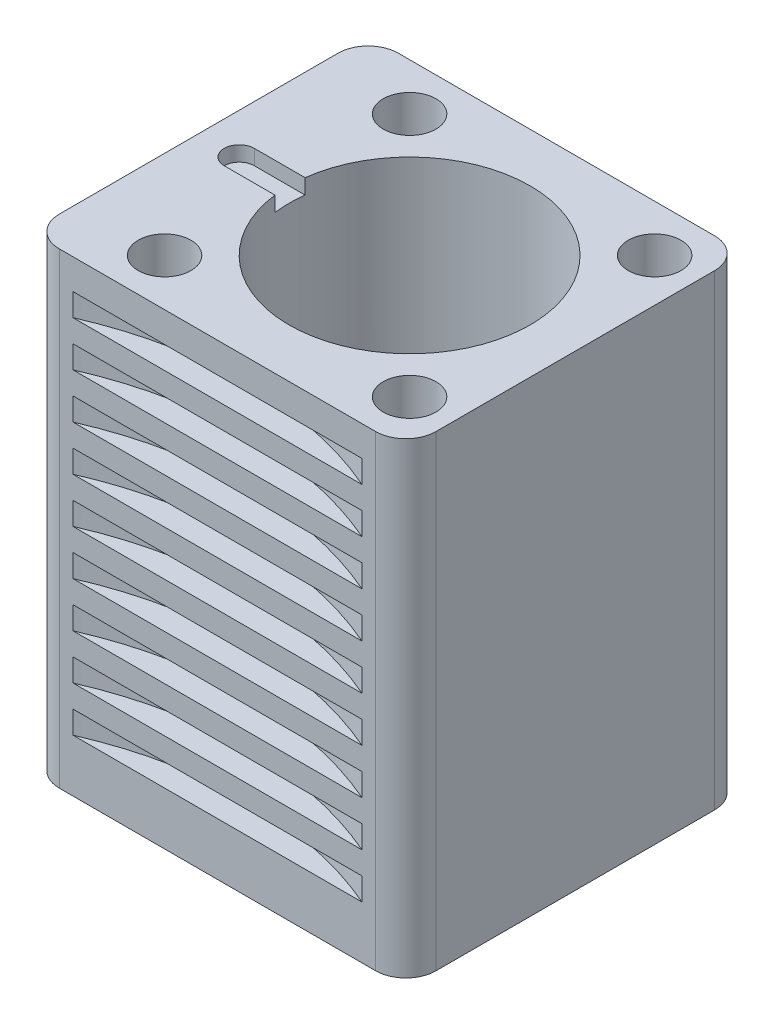
SolidWorks part; units mm, degrees
ref_plane "Front Plane" through (0, 0, 0) normal (0, 0, 1) x (1, 0, 0)
ref_plane "Top Plane" through (0, 0, 0) normal (0, 1, 0) x (1, 0, 0)
ref_plane "Right Plane" through (0, 0, 0) normal (1, 0, 0) x (0, 0, -1)
sketch "Sketch1" plane through (0, 0, 0) normal (0, 1, 0) x (1, 0, 0)
  line L1 (-24, 22.5) -> (18, 22.5)
  line L2 (-28, 18.5) -> (-28, -18.5)
  line L3 (-24, -22.5) -> (18, -22.5)
  line L4 (22, 18.5) -> (22, -18.5)
  line L5 (-28, 22.5) -> (22, -22.5) construction
  line L6 (-28, -22.5) -> (22, 22.5) construction
  arc A0 (18, 22.5) -> (22, 18.5) centre (18, 18.5) cw
  arc A1 (-28, -18.5) -> (-24, -22.5) centre (-24, -18.5) ccw
  arc A2 (18, -22.5) -> (22, -18.5) centre (18, -18.5) ccw
  arc A3 (-24, 22.5) -> (-28, 18.5) centre (-24, 18.5) ccw
  point P4 (-3, 0)
  dimension "D5" = 4
  dimension "D1" = 50
  dimension "D2" = 45
  dimension "D3" = 22
  dimension "D4" = 22.5
extrude "Boss-Extrude1" add sketch "Sketch1" along normal blind 62
sketch "Sketch2" plane through (0, 0, 0) normal (0, -1, 0) x (1, 0, 0)
  circle A0 centre (0, 0) radius 18
  dimension "D1" = 36
extrude "Boss-Extrude2" add sketch "Sketch2" along normal blind 2
sketch "Sketch3" plane through (0, -2, 0) normal (0, -1, 0) x (1, 0, 0)
  circle A0 centre (0, 0) radius 16
  dimension "D1" = 32
extrude "Cut-Extrude1" cut sketch "Sketch3" against normal through all
sketch "Sketch5" plane through (0, 62, 0) normal (0, 1, 0) x (1, 0, 0)
  line L0 (-28, 18.5) -> (-28, -18.5) construction
  line L1 (-22.61, 2) -> (-11.4273, 2)
  line L3 (-22.61, -2) -> (-11.4273, -2)
  line L4 (-11.4273, 2) -> (-11.4273, -2)
  arc A0 (-22.61, 2) -> (-22.61, -2) centre (-22.61, 0) ccw
  point P4 (-16.9989, 0)
  dimension "D1" = 4
  dimension "D2" = 2
  dimension "D3" = 5.39
extrude "Cut-Extrude2" cut sketch "Sketch5" against normal blind 2
sketch "Sketch6" plane through (0, 62, 0) normal (0, 1, 0) x (1, 0, 0)
  line L0 (0, 0) -> (23, 0) construction
  line L1 (0, 0) -> (16.2635, 16.2635) construction
  circle A0 centre (0, 0) radius 23 construction
  circle A1 centre (16.2635, 16.2635) radius 3.5
  circle A2 centre (16.2635, -16.2635) radius 3.5
  circle A3 centre (-16.2635, -16.2635) radius 3.5
  circle A4 centre (-16.2635, 16.2635) radius 3.5
  dimension "D1" = 46
  dimension "D3" = 7
  dimension "D2" = 45
  dimension "D4" = 4
extrude "Cut-Extrude3" cut sketch "Sketch6" against normal through all
ref_plane "Plane1" through (-3, 0, 0) normal (1, 0, 0) x (0, 0, -1)
sketch "Sketch7" plane through (-3, 0, 0) normal (1, 0, 0) x (0, 0, -1)
  line L0 (-22.5, 62) -> (-22.5, 0) construction
  line L5 (-18.5, 58) -> (-66.5, 58)
  line L6 (-18.5, 58) -> (-18.5, 55)
  line L7 (-18.5, 55) -> (-66.5, 55)
  line L8 (-66.5, 58) -> (-66.5, 55)
  line L9 (-18.5, 62) -> (-22.5, 62) construction
  dimension "D1" = 4
  dimension "D2" = 4
  dimension "D3" = 48
  dimension "D4" = 3
revolve "Cut-Revolve1" cut sketch "Sketch7" angle 360 about L8
pattern_linear "LPattern1" count 9 spacing 6 along (0, -1, 0) of "Cut-Revolve1"
mirror "Mirror1" about plane through (0, 0, 0) normal (0, 0, 1) of "LPattern1", "Cut-Revolve1"
sketch "Sketch9" plane through (0, 0, 0) normal (0, 0, 1) x (1, 0, 0)
  line L0 (-24, 62) -> (-28, 62) construction
  line L1 (-24, 58) -> (-72, 58)
  line L2 (-24, 58) -> (-24, 55)
  line L3 (-24, 55) -> (-72, 55)
  line L4 (-72, 58) -> (-72, 55)
  line L5 (-28, 62) -> (-28, 0) construction
  dimension "D1" = 4
  dimension "D2" = 4
  dimension "D3" = 3
  dimension "D4" = 48
revolve "Cut-Revolve3" cut sketch "Sketch9" angle 360 about L4
pattern_linear "LPattern2" count 9 spacing 6 along (0, -1, 0) of "Cut-Revolve3"
